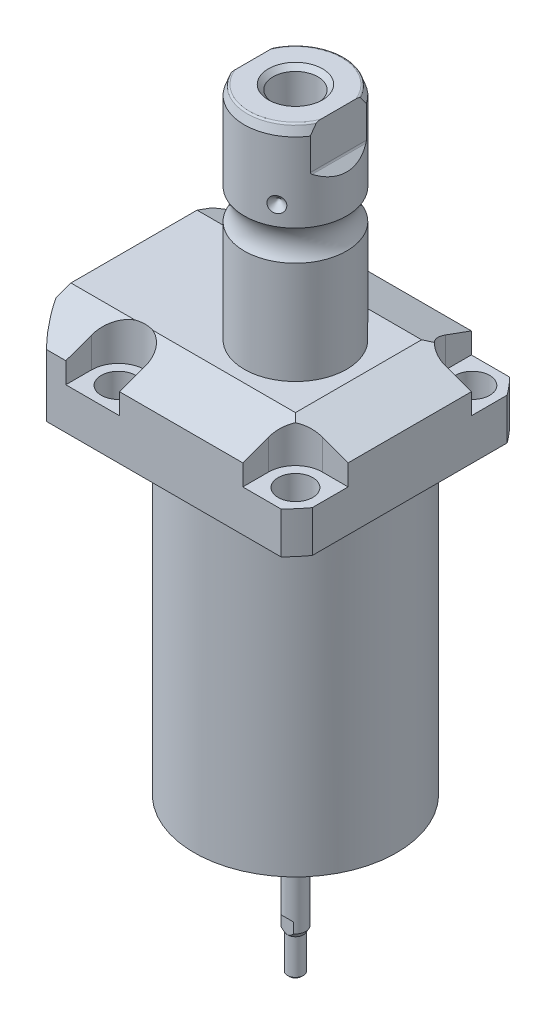
SolidWorks part; units mm, degrees
material "Alloy Steel"
ref_plane "Front Plane" through (0, 0, 0) normal (0, 0, 1) x (1, 0, 0)
ref_plane "Top Plane" through (0, 0, 0) normal (0, 1, 0) x (1, 0, 0)
ref_plane "Right Plane" through (0, 0, 0) normal (1, 0, 0) x (0, 0, -1)
sketch "Sketch1" plane through (0, 0, 0) normal (0, -1, 0) x (0, 0, 1)
  line L0 (-35.433, 50.063) -> (35.433, 50.063)
  line L1 (35.433, 50.063) -> (35.433, -35.433)
  line L2 (35.433, -35.433) -> (-35.433, -35.433)
  line L3 (-35.433, -35.433) -> (-35.433, 50.063)
  line L4 (0, 0) -> (0, -60.6467) construction
  dimension "D1" = 35.433
  dimension "D2" = 85.496
  dimension "D3" = 70.866
extrude "Extrude1" add sketch "Sketch1" against normal blind 122.047
sketch "Sketch2" plane through (0, 0, 0) normal (0, -1, 0) x (1, 0, 0)
  circle A0 centre (-5.4102, 0) radius 50.8
  dimension "D1" = 101.6
  dimension "D2" = 5.4102
extrude "Cut-Extrude1" cut sketch "Sketch2" against normal through all flip side to cut
sketch "Sketch3" plane through (0, 0, 0) normal (1, 0, 0) x (0, 0, -1)
  line L0 (31.3945, 0) -> (31.3945, 96.9518)
  line L1 (31.3945, 96.9518) -> (76.5937, 96.9518)
  line L2 (76.5937, 96.9518) -> (76.5937, 0)
  line L3 (76.5937, 0) -> (31.3945, 0)
  line L4 (0, -93.345) -> (0, 4.445) construction
  line L5 (24.2233, 0) -> (-24.2233, 0) construction
  dimension "D1" = 62.789
  dimension "D2" = 153.1874
  dimension "D3" = 96.9518
revolve "Cut-Revolve1" cut sketch "Sketch3" angle 360 about L4
fillet "Fillet1" radius 0.381 1 edges at (0, 96.9518, -31.3945)
sketch "Sketch4" plane through (0, 122.047, 0) normal (0, 1, 0) x (-1, 0, 0)
  line L0 (-35.433, -30.2072) -> (-35.433, 30.2072) construction
  line L1 (41.8127, 35.433) -> (-30.9923, 35.433) construction
  line L2 (-19.1008, -35.433) -> (-19.1008, -27.432)
  line L3 (-35.433, -35.433) -> (-19.1008, -35.433)
  line L4 (-35.433, -19.1008) -> (-35.433, -35.433)
  line L5 (-27.432, -19.1008) -> (-35.433, -19.1008)
  line L6 (35.7632, -35.433) -> (19.1008, -35.433)
  line L7 (19.1008, 35.433) -> (19.1008, 27.432)
  line L8 (35.7632, 35.433) -> (35.7632, 27.432)
  line L9 (35.7632, 35.433) -> (19.1008, 35.433)
  line L10 (-27.432, 19.1008) -> (-35.433, 19.1008)
  line L11 (-35.433, 19.1008) -> (-35.433, 35.433)
  line L12 (-35.433, 35.433) -> (-19.1008, 35.433)
  line L13 (-19.1008, 35.433) -> (-19.1008, 27.432)
  line L14 (-48.9217, 0) -> (49.4551, 0) construction
  line L15 (35.7632, -35.433) -> (35.7632, -27.432)
  line L16 (19.1008, -35.433) -> (19.1008, -27.432)
  arc A0 (19.1008, -27.432) -> (35.7632, -27.432) centre (27.432, -27.432) cw
  arc A1 (-27.432, -19.1008) -> (-19.1008, -27.432) centre (-27.432, -27.432) cw
  arc A2 (-27.432, 19.1008) -> (-19.1008, 27.432) centre (-27.432, 27.432) ccw
  arc A3 (19.1008, 27.432) -> (35.7632, 27.432) centre (27.432, 27.432) ccw
  dimension "D2" = 8.3312
  dimension "D1" = 27.432
  dimension "D3" = 27.432
  dimension "D4" = 54.864
extrude "Cut-Extrude2" cut sketch "Sketch4" against normal blind 12.243
sketch "Sketch5" plane through (0, 0, 0) normal (1, 0, 0) x (0, 0, -1)
  line L0 (-19.558, 122.047) -> (-35.433, 116.269)
  line L1 (0, 0) -> (0, 154.1081) construction
  line L2 (-19.558, 122.047) -> (-35.433, 122.047)
  line L3 (-35.433, 122.047) -> (-35.433, 116.269)
  dimension "D1" = 15.875
  dimension "D2" = 20
extrude "Cut-Extrude9" cut sketch "Sketch5" against normal through all and the other way through all
mirror "Mirror1" about plane through (0, 0, 0) normal (0, 0, 1) of "Cut-Extrude9"
sketch "Sketch9" plane through (0, 0, 0) normal (0, 0, 1) x (1, 0, 0)
  line L0 (19.558, 122.047) -> (35.433, 116.269)
  line L1 (35.433, 116.269) -> (35.433, 122.047)
  line L2 (35.433, 122.047) -> (19.558, 122.047)
  dimension "D1" = 15.875
  dimension "D2" = 20
extrude "Cut-Extrude7" cut sketch "Sketch9" against normal through all and the other way through all
ref_plane "Plane14" through (-35.0774, 0, 0) normal (1, 0, 0) x (0, 0, -1)
sketch "Sketch20" plane through (-35.0774, 88.9, -18.1102) normal (1, 0, 0) x (0, 1, 0)
  line L0 (-88.9, 18.1102) -> (39.8401, 18.1102) construction
  line L1 (-7.2797, 32.639) -> (36.9042, 32.639) construction
  line L2 (8.0518, 38.3413) -> (9.4996, 38.3413)
  line L3 (8.0518, -6.1131) -> (8.0518, 42.3335) construction
  line L4 (9.4996, 38.3413) -> (9.4996, 35.8902)
  line L5 (9.4996, 35.8902) -> (10.5156, 35.8902)
  line L6 (10.5156, 35.8902) -> (10.5156, 33.8836)
  line L7 (10.5156, 33.8836) -> (21.4884, 33.8836)
  line L8 (21.4884, 33.8836) -> (21.4884, 32.639)
  line L9 (21.4884, 32.639) -> (8.0518, 32.639)
  line L10 (8.0518, 38.3413) -> (8.0518, 32.639)
  dimension "D1" = 14.5288
  dimension "D2" = 11.4046
  dimension "D3" = 1.4478
  dimension "D4" = 6.5024
  dimension "D5" = 1.016
  dimension "D6" = 2.4892
  dimension "D7" = 10.9728
revolve "Cut-Revolve4" cut sketch "Sketch20" angle 360 about L1
mirror "Mirror10" about plane through (0, 0, 0) normal (0, 0, 1) of "Cut-Revolve4"
sketch "Sketch10" plane through (-35.0774, 88.9, -18.1102) normal (1, 0, 0) x (0, 1, 0)
  line L0 (-1.0325, 3.5814) -> (1.5659, 3.5814) construction
  line L1 (21.4884, 4.826) -> (10.5156, 4.826) construction
  line L2 (10.5156, 2.3368) -> (21.4884, 2.3368) construction
  line L4 (8.0518, -12.097) -> (8.0518, 48.3174) construction
  circle A0 centre (8.3185, 8.1026) radius 1.1811
  dimension "D1" = 2.3622
  dimension "D2" = 0.2667
  dimension "D3" = 9.0424
revolve "Revolve4" add sketch "Sketch10" angle 360 about L0
mirror "Mirror12" about plane through (0, 0, 0) normal (0, 0, 1) of bodies 135
sketch "Sketch15" plane through (0, 0, 0) normal (1, 0, 0) x (0, 0, -1)
  line L0 (0, 122.047) -> (15.875, 122.047)
  line L1 (15.875, 122.047) -> (15.875, 153.8139)
  line L2 (15.875, 163.2281) -> (15.875, 187.706)
  line L3 (14.8118, 190.627) -> (0, 190.627)
  line L4 (0, 190.627) -> (0, 122.047)
  line L5 (0, 250.2908) -> (0, 28.9095) construction
  line L6 (19.558, 122.047) -> (-19.558, 122.047) construction
  line L7 (14.8118, 190.627) -> (15.875, 187.706)
  line L9 (24.2233, 96.9518) -> (35.433, 96.9518) construction
  arc A0 (15.875, 163.2281) -> (15.875, 153.8139) centre (22.2504, 158.521) ccw
  dimension "D2" = 20
  dimension "D4" = 7.9248
  dimension "D6" = 28.6512
  dimension "D1" = 93.6752
  dimension "D3" = 31.75
  dimension "D5" = 32.106
  dimension "D7" = 2.921
revolve "Revolve3" add sketch "Sketch15" angle 360 about L5
hole_wizard "Hole1" positions "Sketch18" profile "Sketch17" legacy end condition up to next
sketch "Sketch18" plane through (0, 109.804, 0) normal (0, 1, 0) x (-1, 0, 0)
  arc A0 (35.7632, -27.432) -> (19.1008, -27.432) centre (27.432, -27.432) ccw construction
  arc A1 (19.1008, 27.432) -> (35.7632, 27.432) centre (27.432, 27.432) ccw construction
  arc A2 (-27.432, 19.1008) -> (-19.1008, 27.432) centre (-27.432, 27.432) ccw construction
  arc A3 (-19.1008, -27.432) -> (-27.432, -19.1008) centre (-27.432, -27.432) ccw construction
  point P0 (-27.432, -27.432)
  point P1 (-27.432, 27.432)
  point P3 (27.432, 27.432)
  point P5 (27.432, -27.432)
sketch "Sketch17" plane through (27.432, 109.804, -27.432) normal (1, 0, 0) x (0, 0, 1)
  line L0 (0, 0) -> (0, 12.8522)
  line L1 (0, 12.8522) -> (5.3594, 12.8522)
  line L2 (5.3594, 12.8522) -> (5.3594, 0)
  line L3 (5.3594, 0) -> (0, 0)
  line L4 (0, 110) -> (0, -10) construction
  dimension "Diameter" = 10.7188
  dimension "Depth" = 12.8522
chamfer "Chamfer1" distance 0.635 angle 45 2 edges at (-35.0774, 99.4156, 13.2842) (-35.0774, 99.4156, -13.2842)
ref_plane "Plane15" through (0, 109.4486, 0) normal (0, -1, 0) x (1, 0, 0)
sketch "Sketch21" plane through (0, 109.4486, 0) normal (0, -1, 0) x (1, 0, 0)
  line L0 (-57.5495, -12.9794) -> (-2.9353, -12.9794) construction
  line L1 (-50.063, -1.9304) -> (-49.809, -1.9304)
  line L2 (-49.809, -1.9304) -> (-49.809, -6.7564)
  line L3 (-49.809, -6.7564) -> (-47.2563, -7.4404)
  line L4 (-46.6957, -8.001) -> (-30.759, -8.001)
  line L5 (-30.759, -8.001) -> (-30.759, -12.9794)
  line L6 (-30.759, -12.9794) -> (-50.063, -12.9794)
  line L7 (-50.063, 24.2233) -> (-50.063, -24.2233) construction
  line L8 (-50.063, -12.9794) -> (-50.063, -1.9304)
  line L9 (-47.2563, -7.4404) -> (-46.6957, -8.001)
  dimension "D1" = 12.9794
  dimension "D2" = 0.254
  dimension "D3" = 22.098
  dimension "D4" = 45
  dimension "D5" = 2.5527
  dimension "D6" = 9.9568
  dimension "D7" = 19.05
  dimension "D8" = 15
  dimension "D9" = 12.446
revolve "Cut-Revolve5" cut sketch "Sketch21" angle 360 about L0
mirror "Mirror13" about plane through (0, 0, 0) normal (0, 0, 1) of "Cut-Revolve5"
fillet "Fillet2" radius 0.635 1 edges at (0, 190.627, 14.8118)
sketch "Sketch26" plane through (0, 0, 0) normal (0, 0, 1) x (1, 0, 0)
  line L0 (-39.772, 169.189) -> (35.3173, 169.189) construction
  line L1 (-15.875, 171.602) -> (-13.462, 169.189)
  line L2 (-15.875, 187.706) -> (-15.875, 163.2281) construction
  line L3 (-13.462, 169.189) -> (-15.875, 169.189)
  line L4 (-15.875, 169.189) -> (-15.875, 171.602)
  arc A0 (-15.875, 153.8139) -> (-15.875, 163.2281) centre (-22.2504, 158.521) ccw construction
  dimension "D1" = 45
  dimension "D2" = 4.826
  dimension "D3" = 10.668
revolve "Cut-Revolve7" cut sketch "Sketch26" angle 360 about L0
pattern_circular "CirPattern1" count 3 over 360 about axis through (0, 250.2908, 0) along (0, 1, 0) of "Cut-Revolve7"
hole_wizard "Hole2" positions "Sketch28" profile "Sketch27" legacy
sketch "Sketch28" plane through (0, 190.627, 0) normal (0, 1, 0) x (-1, 0, 0)
  circle A0 centre (0, 0) radius 15.875 construction
  point P0 (0, 0)
sketch "Sketch27" plane through (0, 190.627, 0) normal (1, 0, 0) x (0, 0, 1)
  line L0 (0, 0) -> (0, 28.8121)
  line L1 (0, 28.8121) -> (6.9469, 24.638)
  line L2 (6.9469, 24.638) -> (6.9469, 0)
  line L4 (6.9469, 0) -> (0, 0)
  line L6 (0, 28.8121) -> (-6.9469, 24.638) construction
  line L7 (0, -4.2442) -> (0, 117.3081) construction
  dimension "Diameter" = 13.8938
  dimension "Depth" = 24.638
  dimension "Drill Angle" = 118
sketch "Sketch29" plane through (0, 0, 0) normal (0, 0, 1) x (1, 0, 0)
  line L0 (0, 0) -> (0, 192.0172) construction
  line L1 (13.284, 190.627) -> (13.284, 177.927)
  line L2 (14.3672, 190.627) -> (-14.3672, 190.627) construction
  line L3 (13.5072, 177.3882) -> (16.332, 174.5634)
  line L5 (16.332, 174.5634) -> (16.332, 190.627)
  line L6 (16.332, 190.627) -> (13.284, 190.627)
  line L7 (-16.332, 190.627) -> (-13.284, 190.627)
  line L8 (-16.332, 174.5634) -> (-16.332, 190.627)
  line L9 (-13.5072, 177.3882) -> (-16.332, 174.5634)
  line L10 (-13.284, 190.627) -> (-13.284, 177.927)
  arc A0 (13.284, 177.927) -> (13.5072, 177.3882) centre (14.046, 177.927) ccw
  arc A1 (-13.284, 177.927) -> (-13.5072, 177.3882) centre (-14.046, 177.927) cw
  dimension "D2" = 0.762
  dimension "D1" = 45
  dimension "D3" = 26.568
  dimension "D4" = 12.7
  dimension "D5" = 3.048
extrude "Cut-Extrude10" cut sketch "Sketch29" against normal through all and the other way through all
chamfer "Chamfer2" distance 1.4351 angle 45 1 edges at (0, 190.627, 6.9469)
sketch "Sketch30" plane through (0, 0, 0) normal (0, -1, 0) x (1, 0, 0)
  line L0 (0, 0) -> (18.7689, -5.0291) construction
  line L2 (47.0228, 0) -> (-47.0228, 0) construction
  line L3 (0, 0) -> (-9.7155, -16.8277) construction
  line L4 (0, 0) -> (-13.7398, -13.7398) construction
  line L5 (0, 0) -> (-9.7155, 16.8277) construction
  line L7 (0, 0) -> (-5.0291, 18.7689) construction
  circle A0 centre (0, 0) radius 19.431 construction
  circle A1 centre (19.431, 0) radius 1.27
  circle A2 centre (18.7689, -5.0291) radius 1.27
  circle A3 centre (-9.7155, -16.8277) radius 1.27
  circle A4 centre (-13.7398, -13.7398) radius 1.27
  circle A5 centre (-9.7155, 16.8277) radius 1.27
  circle A6 centre (-5.0291, 18.7689) radius 1.27
  dimension "D1" = 38.862
  dimension "D7" = 2.54
  dimension "D8" = 2.54
  dimension "D9" = 2.54
  dimension "D10" = 2.54
  dimension "D11" = 2.54
  dimension "D12" = 2.54
  dimension "D2" = 15
  dimension "D3" = 120
  dimension "D4" = 15
  dimension "D5" = 120
  dimension "D6" = 15
extrude "Cut-Extrude11" cut sketch "Sketch30" against normal blind 7.62
sketch "Sketch31" plane through (0, 0, 0) normal (1, 0, 0) x (0, 0, -1)
  line L0 (0, 61.6176) -> (0, -19.4362) construction
  line L2 (14.351, 0) -> (14.351, 1.3208)
  line L3 (-31.3945, 0) -> (31.3945, 0) construction
  line L4 (14.351, 1.3208) -> (11.6459, 1.3208)
  line L5 (11.6459, 1.3208) -> (11.6459, 0)
  line L6 (11.6459, 0) -> (14.351, 0)
  dimension "D1" = 1.3208
  dimension "D2" = 28.702
  dimension "D3" = 23.2918
revolve "Cut-Revolve8" cut sketch "Sketch31" angle 360 about L0
sketch "Sketch32" plane through (0, 0, 0) normal (1, 0, 0) x (0, 0, -1)
  line L0 (0, 46.6429) -> (0, -27.2479) construction
  line L2 (3.175, 0) -> (3.175, -35.2494)
  line L3 (-31.3945, 0) -> (31.3945, 0) construction
  line L4 (3.175, -35.2494) -> (2.4384, -36.5252)
  line L5 (2.4384, -36.5252) -> (2.4384, -47.4472)
  line L6 (2.4384, -47.4472) -> (1.9304, -47.9552)
  line L7 (1.9304, -47.9552) -> (0, -47.9552)
  line L8 (0, -47.9552) -> (0, 0)
  line L9 (0, 0) -> (3.175, 0)
  line L10 (-5.4728, 190.627) -> (-14.3672, 190.627) construction
  dimension "D1" = 6.35
  dimension "D2" = 4.8768
  dimension "D3" = 30
  dimension "D4" = 11.43
  dimension "D5" = 45
  dimension "D6" = 0.508
  dimension "D7" = 238.5822
revolve "Revolve5" add sketch "Sketch32" angle 360 about L0
sketch "Sketch33" plane through (0, 0, 0) normal (1, 0, 0) x (0, 0, -1)
  line L0 (2.5019, -36.4152) -> (2.5019, -32.0802)
  line L4 (2.4384, -36.5252) -> (3.175, -35.2494) construction
  line L7 (2.5019, -32.0802) -> (3.2639, -31.3182)
  line L12 (3.2639, -31.3182) -> (3.2639, -36.4152)
  line L13 (2.5019, -36.4152) -> (3.2639, -36.4152)
  line L14 (0, 47.0228) -> (0, -47.0228) construction
  line L15 (-1.9304, -47.9552) -> (1.9304, -47.9552) construction
  dimension "D1" = 2.5019
  dimension "D2" = 45
  dimension "D3" = 0.762
  dimension "D4" = 15.875
extrude "Cut-Extrude12" cut sketch "Sketch33" against normal mid plane 6.35
mirror "Mirror14" about plane through (0, 0, 0) normal (0, 0, 1) of "Cut-Extrude12"
